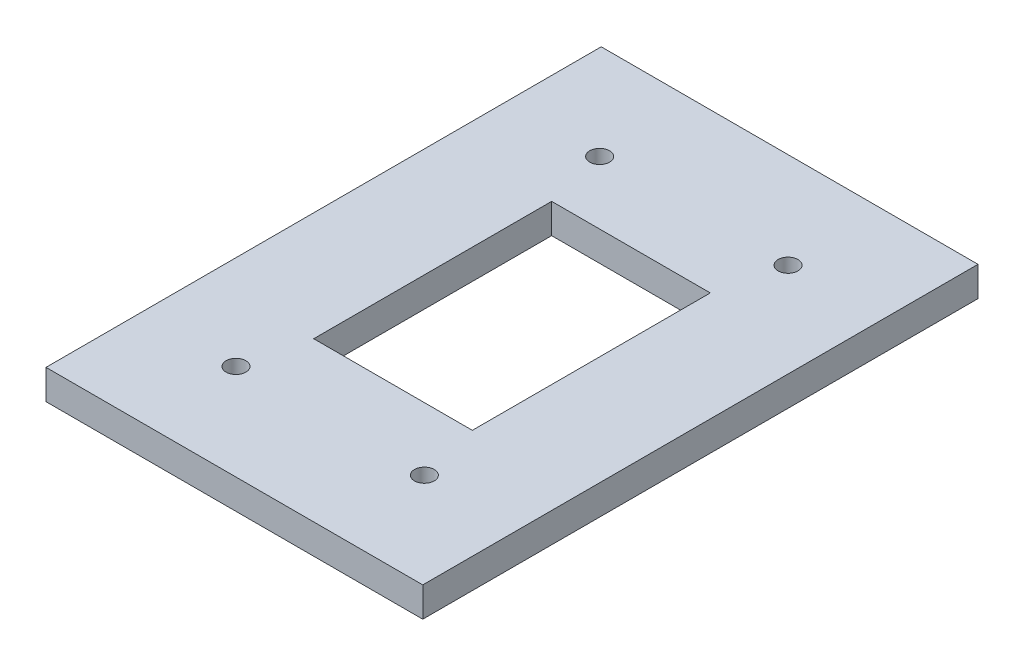
SolidWorks part; units mm, degrees
ref_plane "Front Plane" through (0, 0, 0) normal (0, 0, 1) x (1, 0, 0)
ref_plane "Top Plane" through (0, 0, 0) normal (0, 1, 0) x (1, 0, 0)
ref_plane "Right Plane" through (0, 0, 0) normal (1, 0, 0) x (0, 0, -1)
sketch "Sketch1" plane through (0, 0, 0) normal (0, 1, 0) x (1, 0, 0)
  line L1 (120.65, 177.8) -> (-120.65, 177.8)
  line L2 (120.65, 177.8) -> (120.65, -177.8)
  line L3 (120.65, -177.8) -> (-120.65, -177.8)
  line L4 (-120.65, 177.8) -> (-120.65, -177.8)
  line L5 (120.65, 177.8) -> (-120.65, -177.8) construction
  line L6 (120.65, -177.8) -> (-120.65, 177.8) construction
  point P0 (0, 0)
  dimension "D1" = 241.3
  dimension "D2" = 355.6
extrude "Boss-Extrude1" add sketch "Sketch1" along normal mid plane 19.05
sketch "Sketch2" plane through (0, 9.525, 0) normal (0, 1, 0) x (1, 0, 0)
  line L0 (0, 177.8) -> (0, -177.8) construction
  line L1 (120.65, 177.8) -> (-120.65, 177.8) construction
  line L2 (-120.65, -177.8) -> (120.65, -177.8) construction
  line L3 (-120.65, 0) -> (120.65, 0) construction
  line L4 (-120.65, 177.8) -> (-120.65, -177.8) construction
  line L5 (120.65, -177.8) -> (120.65, 177.8) construction
  circle A0 centre (-60.325, 116.459) radius 6.35
  circle A3 centre (60.325, 116.459) radius 6.35
  circle A4 centre (60.325, -116.459) radius 6.35
  circle A5 centre (-60.325, -116.459) radius 6.35
  dimension "D3" = 12.7
  dimension "D1" = 120.65
  dimension "D2" = 232.918
extrude "Cut-Extrude1" cut sketch "Sketch2" against normal through all
sketch "Sketch3" plane through (0, 9.525, 0) normal (0, 1, 0) x (1, 0, 0)
  line L1 (-50.8, -76.2) -> (50.8, -76.2)
  line L2 (-50.8, -76.2) -> (-50.8, 76.2)
  line L3 (-50.8, 76.2) -> (50.8, 76.2)
  line L4 (50.8, -76.2) -> (50.8, 76.2)
  line L5 (-50.8, -76.2) -> (50.8, 76.2) construction
  line L6 (-50.8, 76.2) -> (50.8, -76.2) construction
  point P0 (0, 0)
  dimension "D1" = 101.6
  dimension "D2" = 152.4
extrude "Cut-Extrude2" cut sketch "Sketch3" against normal through all and the other way through all
